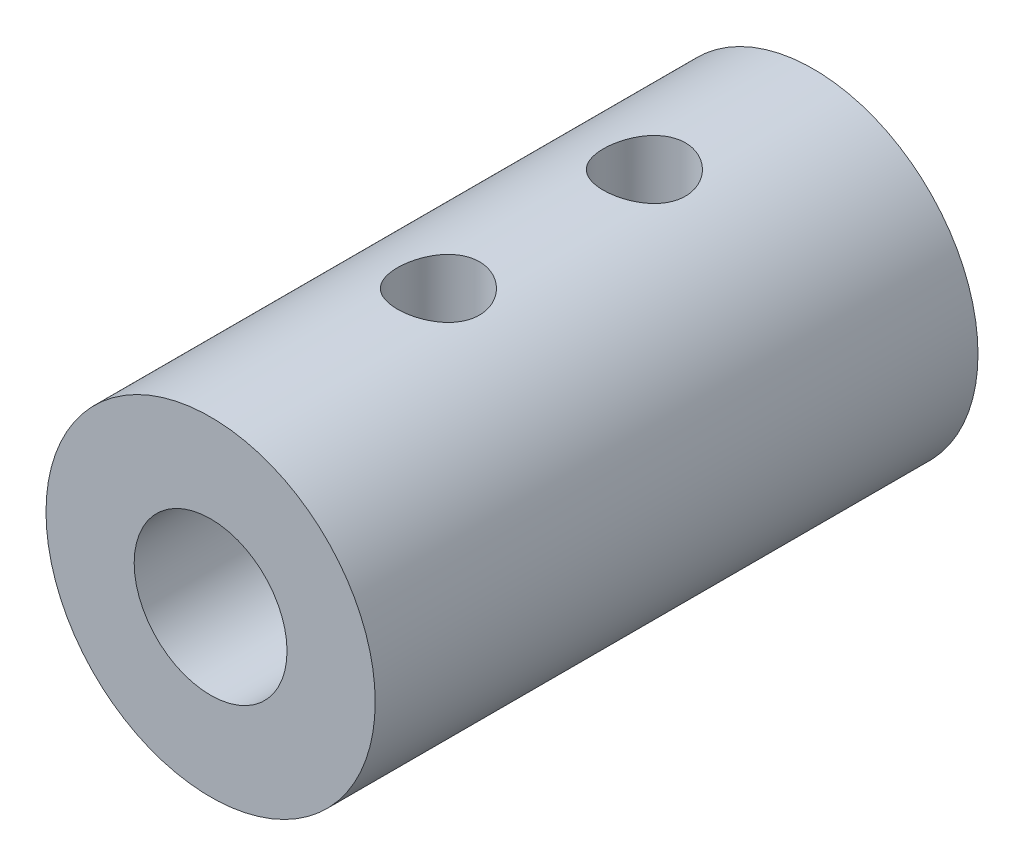
SolidWorks part; units mm, degrees
ref_plane "Front Plane" through (0, 0, 0) normal (0, 0, 1) x (1, 0, 0)
ref_plane "Top Plane" through (0, 0, 0) normal (0, 1, 0) x (1, 0, 0)
ref_plane "Right Plane" through (0, 0, 0) normal (1, 0, 0) x (0, 0, -1)
sketch "Sketch1" plane through (0, 0, 0) normal (0, 0, 1) x (1, 0, 0)
  circle A0 centre (0, 0) radius 2.6
  circle A1 centre (0, 0) radius 5.6
  dimension "D1" = 3
extrude "Boss-Extrude1" add sketch "Sketch1" along normal offset from surface 10 and the other way offset from surface (9 mm away) 5
sketch "Sketch3" plane through (0, 0, 0) normal (0, 1, 0) x (1, 0, 0)
  line L0 (0, -3.758) -> (0, -0.508) construction
  line L1 (2.25, -0.508) -> (-2.25, -0.508) construction
  line L2 (0, 0) -> (0, 3.25) construction
  circle A1 centre (0, -3.758) radius 1.397
  circle A3 centre (0, 3.25) radius 1.397
  dimension "D2" = 2.794
  dimension "D1" = 3.25
extrude "Cut-Extrude2" cut sketch "Sketch3" along normal through all
